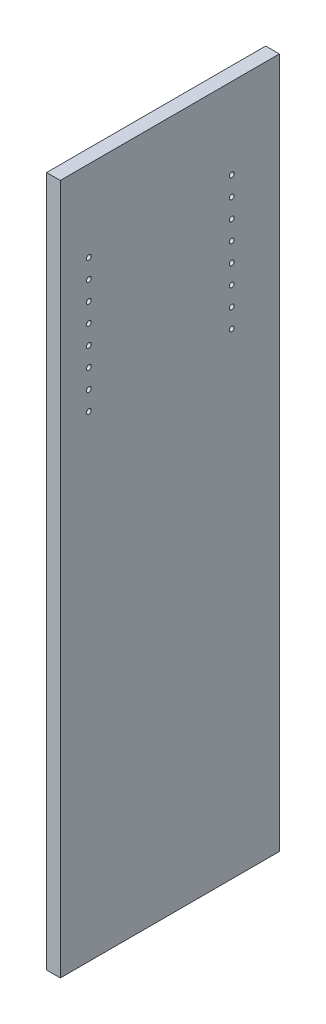
SolidWorks part; units mm, degrees
material "Cedar"
ref_plane "Front Plane" through (0, 0, 0) normal (0, 0, 1) x (1, 0, 0)
ref_plane "Top Plane" through (0, 0, 0) normal (0, 1, 0) x (1, 0, 0)
ref_plane "Right Plane" through (0, 0, 0) normal (1, 0, 0) x (0, 0, -1)
sketch "Sketch1" plane through (0, 0, 0) normal (1, 0, 0) x (0, 0, -1)
  line L1 (-146.05, -460.375) -> (146.05, -460.375)
  line L2 (-146.05, -460.375) -> (-146.05, 460.375)
  line L3 (-146.05, 460.375) -> (146.05, 460.375)
  line L4 (146.05, -460.375) -> (146.05, 460.375)
  line L5 (-146.05, -460.375) -> (146.05, 460.375) construction
  line L6 (-146.05, 460.375) -> (146.05, -460.375) construction
  point P0 (0, 0)
  dimension "D1" = 292.1
  dimension "D2" = 920.75
extrude "Boss-Extrude1" add sketch "Sketch1" along normal blind 18.2562
sketch "Sketch3" plane through (18.2562, 0, 0) normal (1, 0, 0) x (0, 0, -1)
  line L0 (-107.95, 460.375) -> (-107.95, -460.375) construction
  line L1 (146.05, 460.375) -> (-146.05, 460.375) construction
  line L2 (-146.05, -460.375) -> (146.05, -460.375) construction
  line L3 (-12.7, 460.375) -> (-12.7, -460.375) construction
  line L4 (-146.05, 460.375) -> (-146.05, -460.375) construction
  line L5 (0, 0) -> (-12.7, 0) construction
  line L6 (-12.7, 0) -> (-107.95, 0) construction
  circle A0 centre (-107.95, 352.425) radius 3.175
  circle A1 centre (-107.95, 327.025) radius 3.175
  circle A2 centre (-107.95, 301.625) radius 3.175
  circle A3 centre (-107.95, 276.225) radius 3.175
  circle A4 centre (-107.95, 250.825) radius 3.175
  circle A5 centre (-107.95, 225.425) radius 3.175
  circle A6 centre (-107.95, 200.025) radius 3.175
  circle A7 centre (-107.95, 174.625) radius 3.175
  circle A32 centre (82.55, 174.625) radius 3.175
  circle A33 centre (82.55, 200.025) radius 3.175
  circle A34 centre (82.55, 225.425) radius 3.175
  circle A35 centre (82.55, 250.825) radius 3.175
  circle A36 centre (82.55, 276.225) radius 3.175
  circle A37 centre (82.55, 301.625) radius 3.175
  circle A38 centre (82.55, 327.025) radius 3.175
  circle A39 centre (82.55, 352.425) radius 3.175
  dimension "D1" = 6.35
  dimension "D2" = 38.1
  dimension "D3" = 107.95
  dimension "D5" = 25.4
  dimension "D6" = 12.7
  dimension "D4" = 8
extrude "Cut-Extrude1" cut sketch "Sketch3" against normal blind 9.525
